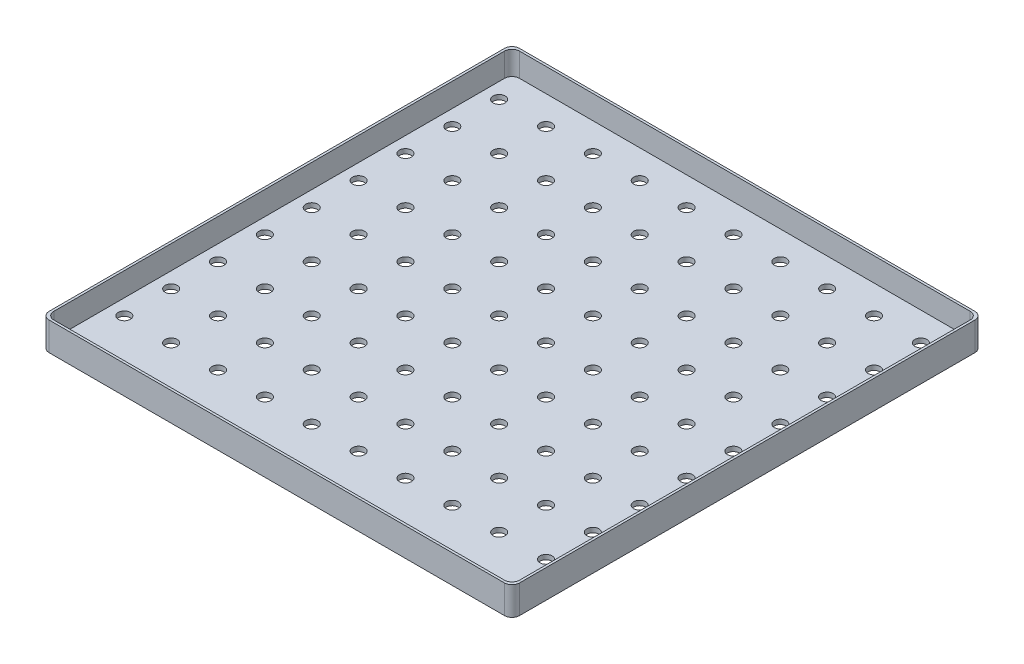
SolidWorks part; units mm, degrees
ref_plane "Front Plane" through (0, 0, 0) normal (0, 0, 1) x (1, 0, 0)
ref_plane "Top Plane" through (0, 0, 0) normal (0, 1, 0) x (1, 0, 0)
ref_plane "Right Plane" through (0, 0, 0) normal (1, 0, 0) x (0, 0, -1)
sketch "Sketch1" plane through (0, 0, 0) normal (0, 1, 0) x (1, 0, 0)
  line L1 (-139.1167, 137.224) -> (109.8833, 137.224)
  line L2 (-139.1167, 137.224) -> (-139.1167, -111.776)
  line L3 (-139.1167, -111.776) -> (109.8833, -111.776)
  line L4 (109.8833, 137.224) -> (109.8833, -111.776)
  dimension "D1" = 249
  dimension "D2" = 249
extrude "Boss-Extrude1" add sketch "Sketch1" along normal blind 2.5
sketch "Sketch2" plane through (0, 2.5, 0) normal (0, 1, 0) x (1, 0, 0)
  line L0 (-14.6167, 137.224) -> (-14.6167, -111.776) construction
  line L1 (109.8833, 137.224) -> (-139.1167, 137.224) construction
  line L2 (-139.1167, -111.776) -> (109.8833, -111.776) construction
  line L3 (-139.1167, 12.724) -> (109.8833, 12.724) construction
  line L4 (-139.1167, 137.224) -> (-139.1167, -111.776) construction
  line L5 (109.8833, -111.776) -> (109.8833, 137.224) construction
  line L7 (-137.8667, -110.526) -> (108.6333, -110.526)
  line L8 (-137.8667, -110.526) -> (-137.8667, 135.974)
  line L9 (-137.8667, 135.974) -> (108.6333, 135.974)
  line L10 (108.6333, -110.526) -> (108.6333, 135.974)
  line L11 (-137.8667, -110.526) -> (108.6333, 135.974) construction
  line L12 (-137.8667, 135.974) -> (108.6333, -110.526) construction
  line L13 (-139.1167, -111.776) -> (109.8833, -111.776)
  line L14 (-139.1167, -111.776) -> (-139.1167, 137.224)
  line L15 (-139.1167, 137.224) -> (109.8833, 137.224)
  line L16 (109.8833, -111.776) -> (109.8833, 137.224)
  line L17 (-139.1167, -111.776) -> (109.8833, 137.224) construction
  line L18 (-139.1167, 137.224) -> (109.8833, -111.776) construction
  point P12 (-14.6167, 12.724)
  point P17 (-14.6167, 12.724)
  dimension "D1" = 246.5
  dimension "D2" = 246.5
extrude "Boss-Extrude2" add sketch "Sketch2" along normal blind 12.5
fillet "Fillet1" radius 4 4 edges at (109.8833, 7.5, 111.776) (109.8833, 7.5, -137.224) (-139.1167, 7.5, -137.224) (-139.1167, 7.5, 111.776)
fillet "Fillet2" radius 4 4 edges at (108.6333, 8.75, 110.526) (108.6333, 8.75, -135.974) (-137.8667, 8.75, -135.974) (-137.8667, 8.75, 110.526)
sketch "Sketch3" plane through (0, 0, 0) normal (0, -1, 0) x (1, 0, 0)
  line L0 (-129.6167, 102.276) -> (-129.6167, -128.224) construction
  line L1 (-135.1167, 111.776) -> (105.8833, 111.776) construction
  line L2 (105.8833, -137.224) -> (-135.1167, -137.224) construction
  line L3 (-139.1167, -133.224) -> (-139.1167, 107.776) construction
  line L4 (-104.8167, 102.276) -> (-104.8167, -128.224) construction
  line L5 (-80.0167, 102.276) -> (-80.0167, -128.224) construction
  line L6 (-55.2167, 102.276) -> (-55.2167, -128.224) construction
  line L7 (-30.4167, 102.276) -> (-30.4167, -128.224) construction
  line L8 (-5.6167, 102.276) -> (-5.6167, -128.224) construction
  line L9 (19.1833, 102.276) -> (19.1833, -128.224) construction
  line L10 (43.9833, 102.276) -> (43.9833, -128.224) construction
  line L11 (68.7833, 102.276) -> (68.7833, -128.224) construction
  line L12 (93.5833, 102.276) -> (93.5833, -128.224) construction
  circle A0 centre (-129.6167, 102.276) radius 3.2
  circle A1 centre (-129.6167, 77.476) radius 3.2
  circle A2 centre (-129.6167, 52.676) radius 3.2
  circle A3 centre (-129.6167, 27.876) radius 3.2
  circle A4 centre (-129.6167, 3.076) radius 3.2
  circle A5 centre (-129.6167, -21.724) radius 3.2
  circle A6 centre (-129.6167, -46.524) radius 3.2
  circle A7 centre (-129.6167, -71.324) radius 3.2
  circle A8 centre (-129.6167, -96.124) radius 3.2
  circle A9 centre (-129.6167, -120.924) radius 3.2
  circle A10 centre (-104.8167, 102.276) radius 3.2
  circle A11 centre (-104.8167, 77.476) radius 3.2
  circle A12 centre (-104.8167, 52.676) radius 3.2
  circle A13 centre (-104.8167, 27.876) radius 3.2
  circle A14 centre (-104.8167, 3.076) radius 3.2
  circle A15 centre (-104.8167, -21.724) radius 3.2
  circle A16 centre (-104.8167, -46.524) radius 3.2
  circle A17 centre (-104.8167, -71.324) radius 3.2
  circle A18 centre (-104.8167, -96.124) radius 3.2
  circle A19 centre (-104.8167, -120.924) radius 3.2
  circle A20 centre (-80.0167, 102.276) radius 3.2
  circle A21 centre (-80.0167, 77.476) radius 3.2
  circle A22 centre (-80.0167, 52.676) radius 3.2
  circle A23 centre (-80.0167, 27.876) radius 3.2
  circle A24 centre (-80.0167, 3.076) radius 3.2
  circle A25 centre (-80.0167, -21.724) radius 3.2
  circle A26 centre (-80.0167, -46.524) radius 3.2
  circle A27 centre (-80.0167, -71.324) radius 3.2
  circle A28 centre (-80.0167, -96.124) radius 3.2
  circle A29 centre (-80.0167, -120.924) radius 3.2
  circle A30 centre (-55.2167, 102.276) radius 3.2
  circle A31 centre (-55.2167, 77.476) radius 3.2
  circle A32 centre (-55.2167, 52.676) radius 3.2
  circle A33 centre (-55.2167, 27.876) radius 3.2
  circle A34 centre (-55.2167, 3.076) radius 3.2
  circle A35 centre (-55.2167, -21.724) radius 3.2
  circle A36 centre (-55.2167, -46.524) radius 3.2
  circle A37 centre (-55.2167, -71.324) radius 3.2
  circle A38 centre (-55.2167, -96.124) radius 3.2
  circle A39 centre (-55.2167, -120.924) radius 3.2
  circle A40 centre (-30.4167, 102.276) radius 3.2
  circle A41 centre (-30.4167, 77.476) radius 3.2
  circle A42 centre (-30.4167, 52.676) radius 3.2
  circle A43 centre (-30.4167, 27.876) radius 3.2
  circle A44 centre (-30.4167, 3.076) radius 3.2
  circle A45 centre (-30.4167, -21.724) radius 3.2
  circle A46 centre (-30.4167, -46.524) radius 3.2
  circle A47 centre (-30.4167, -71.324) radius 3.2
  circle A48 centre (-30.4167, -96.124) radius 3.2
  circle A49 centre (-30.4167, -120.924) radius 3.2
  circle A50 centre (-5.6167, 102.276) radius 3.2
  circle A51 centre (-5.6167, 77.476) radius 3.2
  circle A52 centre (-5.6167, 52.676) radius 3.2
  circle A53 centre (-5.6167, 27.876) radius 3.2
  circle A54 centre (-5.6167, 3.076) radius 3.2
  circle A55 centre (-5.6167, -21.724) radius 3.2
  circle A56 centre (-5.6167, -46.524) radius 3.2
  circle A57 centre (-5.6167, -71.324) radius 3.2
  circle A58 centre (-5.6167, -96.124) radius 3.2
  circle A59 centre (-5.6167, -120.924) radius 3.2
  circle A60 centre (19.1833, 102.276) radius 3.2
  circle A61 centre (19.1833, 77.476) radius 3.2
  circle A62 centre (19.1833, 52.676) radius 3.2
  circle A63 centre (19.1833, 27.876) radius 3.2
  circle A64 centre (19.1833, 3.076) radius 3.2
  circle A65 centre (19.1833, -21.724) radius 3.2
  circle A66 centre (19.1833, -46.524) radius 3.2
  circle A67 centre (19.1833, -71.324) radius 3.2
  circle A68 centre (19.1833, -96.124) radius 3.2
  circle A69 centre (19.1833, -120.924) radius 3.2
  circle A70 centre (43.9833, 102.276) radius 3.2
  circle A71 centre (43.9833, 77.476) radius 3.2
  circle A72 centre (43.9833, 52.676) radius 3.2
  circle A73 centre (43.9833, 27.876) radius 3.2
  circle A74 centre (43.9833, 3.076) radius 3.2
  circle A75 centre (43.9833, -21.724) radius 3.2
  circle A76 centre (43.9833, -46.524) radius 3.2
  circle A77 centre (43.9833, -71.324) radius 3.2
  circle A78 centre (43.9833, -96.124) radius 3.2
  circle A79 centre (43.9833, -120.924) radius 3.2
  circle A80 centre (68.7833, 102.276) radius 3.2
  circle A81 centre (68.7833, 77.476) radius 3.2
  circle A82 centre (68.7833, 52.676) radius 3.2
  circle A83 centre (68.7833, 27.876) radius 3.2
  circle A84 centre (68.7833, 3.076) radius 3.2
  circle A85 centre (68.7833, -21.724) radius 3.2
  circle A86 centre (68.7833, -46.524) radius 3.2
  circle A87 centre (68.7833, -71.324) radius 3.2
  circle A88 centre (68.7833, -96.124) radius 3.2
  circle A89 centre (68.7833, -120.924) radius 3.2
  circle A90 centre (93.5833, 102.276) radius 3.2
  circle A91 centre (93.5833, 77.476) radius 3.2
  circle A92 centre (93.5833, 52.676) radius 3.2
  circle A93 centre (93.5833, 27.876) radius 3.2
  circle A94 centre (93.5833, 3.076) radius 3.2
  circle A95 centre (93.5833, -21.724) radius 3.2
  circle A96 centre (93.5833, -46.524) radius 3.2
  circle A97 centre (93.5833, -71.324) radius 3.2
  circle A98 centre (93.5833, -96.124) radius 3.2
  circle A99 centre (93.5833, -120.924) radius 3.2
  dimension "D4" = 10
  dimension "D1" = 9.5
  dimension "D2" = 9
  dimension "D3" = 9.5
  dimension "D5" = 10
extrude "Cut-Extrude1" cut sketch "Sketch3" against normal blind 12.5
